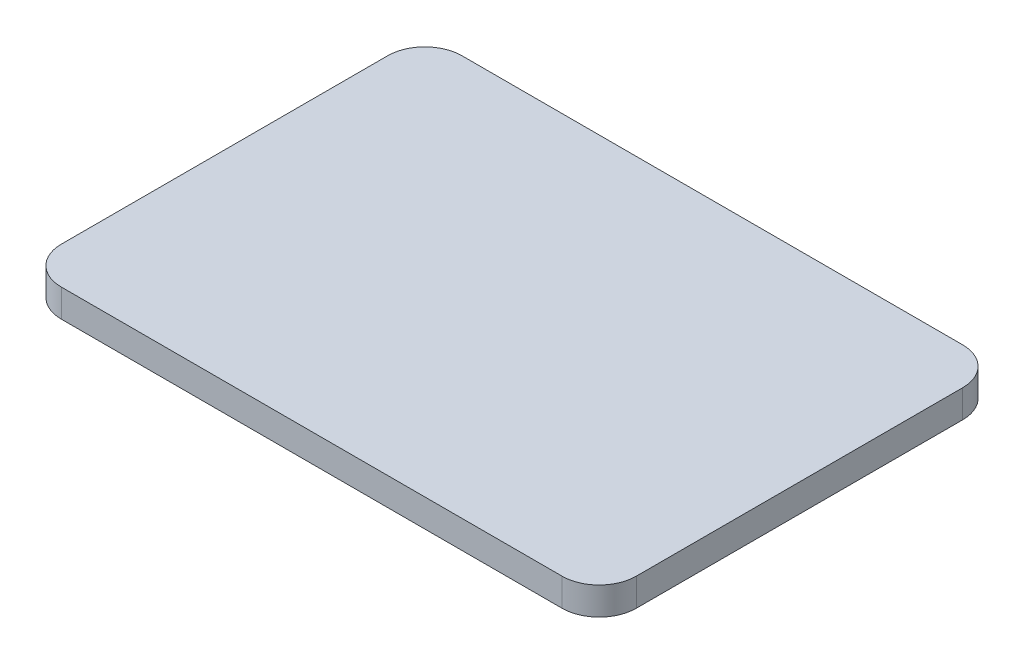
SolidWorks part; units mm, degrees
ref_plane "Спереди" through (0, 0, 0) normal (0, 0, 1) x (1, 0, 0)
ref_plane "Сверху" through (0, 0, 0) normal (0, 1, 0) x (1, 0, 0)
ref_plane "Справа" through (0, 0, 0) normal (1, 0, 0) x (0, 0, -1)
sketch "Эскиз1" plane through (0, 0, 0) normal (0, 1, 0) x (1, 0, 0)
  line L1 (-135, 108) -> (135, 108)
  line L2 (-155, 88) -> (-155, -88)
  line L3 (-135, -108) -> (135, -108)
  line L4 (155, 88) -> (155, -88)
  line L5 (-155, 108) -> (155, -108) construction
  line L6 (-155, -108) -> (155, 108) construction
  arc A0 (-135, 108) -> (-155, 88) centre (-135, 88) ccw
  arc A1 (-155, -88) -> (-135, -108) centre (-135, -88) ccw
  arc A2 (135, -108) -> (155, -88) centre (135, -88) ccw
  arc A3 (135, 108) -> (155, 88) centre (135, 88) cw
  point P0 (0, 0)
  dimension "D1" = 20
  dimension "D2" = 20
  dimension "D3" = 216
  dimension "D4" = 310
extrude "Бобышка-Вытянуть1" add sketch "Эскиз1" along normal blind 15
